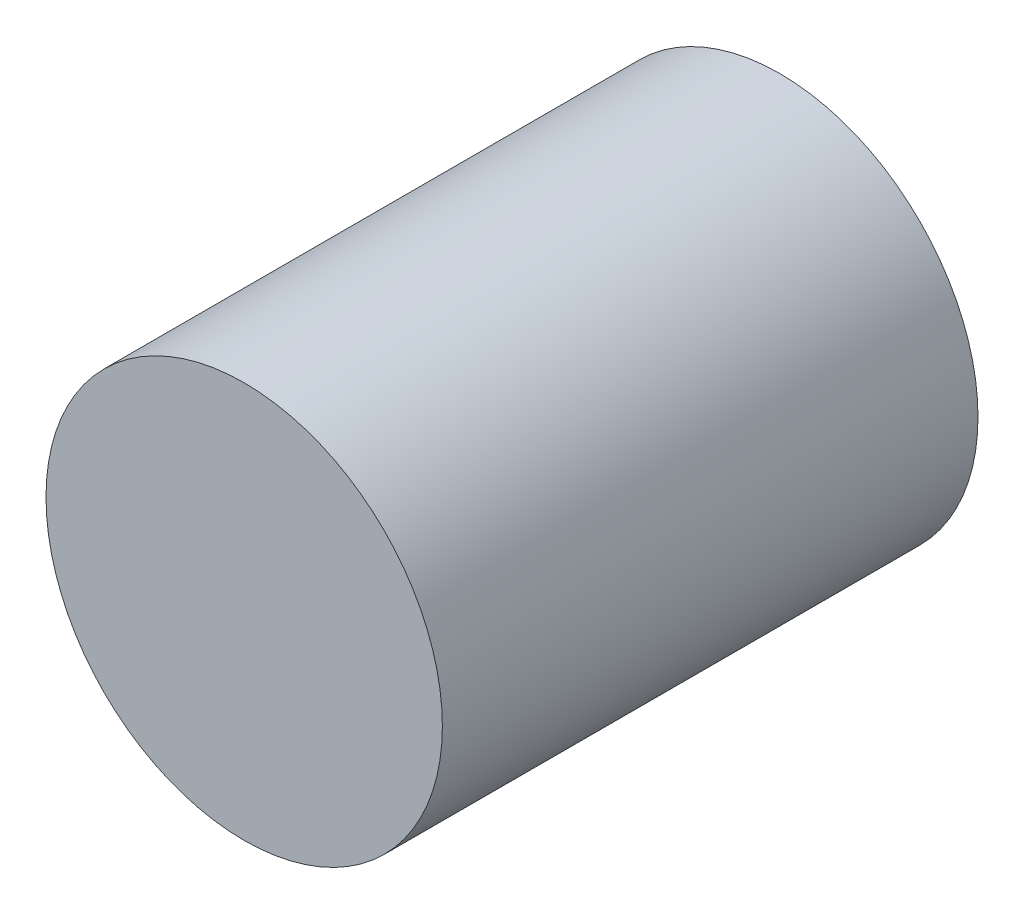
SolidWorks part; units mm, degrees
ref_plane "Front Plane" through (0, 0, 0) normal (0, 0, 1) x (1, 0, 0)
ref_plane "Top Plane" through (0, 0, 0) normal (0, 1, 0) x (1, 0, 0)
ref_plane "Right Plane" through (0, 0, 0) normal (1, 0, 0) x (0, 0, -1)
sketch "Sketch2" plane through (0, 0, 0) normal (0, 0, 1) x (1, 0, 0)
  circle A0 centre (0, 0) radius 4.699
  dimension "D1" = 9.398
extrude "Boss-Extrude1" add sketch "Sketch2" along normal blind 12.7
scale "Scale1" scale about centroid uniform scaling yes scale factor 0.65
